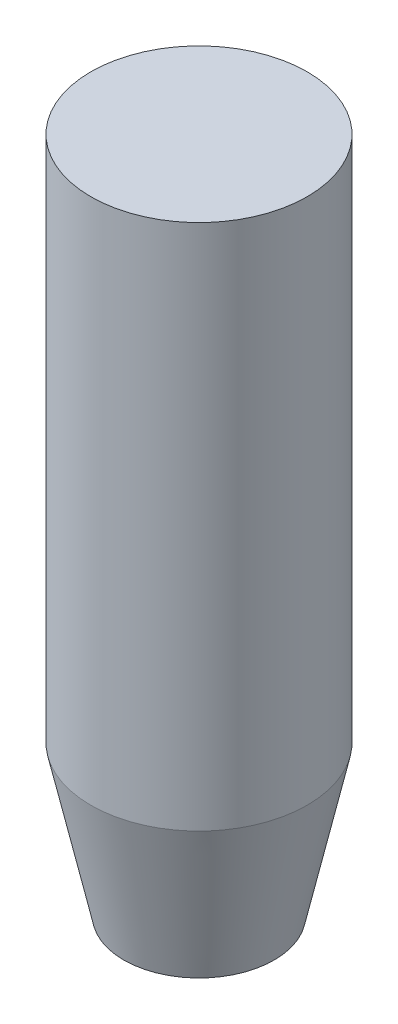
SolidWorks part; units mm, degrees
material "6061-T6 (SS)"
ref_plane "Front Plane" through (0, 0, 0) normal (0, 0, 1) x (1, 0, 0)
ref_plane "Top Plane" through (0, 0, 0) normal (0, 1, 0) x (1, 0, 0)
ref_plane "Right Plane" through (0, 0, 0) normal (1, 0, 0) x (0, 0, -1)
sketch "Sketch1" plane through (0, 0, 0) normal (0, 1, 0) x (1, 0, 0)
  circle A0 centre (0, 0) radius 18.2562
  dimension "D1" = 36.5125
extrude "Boss-Extrude1" add sketch "Sketch1" along normal blind 114.3
chamfer "Chamfer1" distance 5.5562 distance2 25.4 1 edges at (0, 0, 18.2562)
